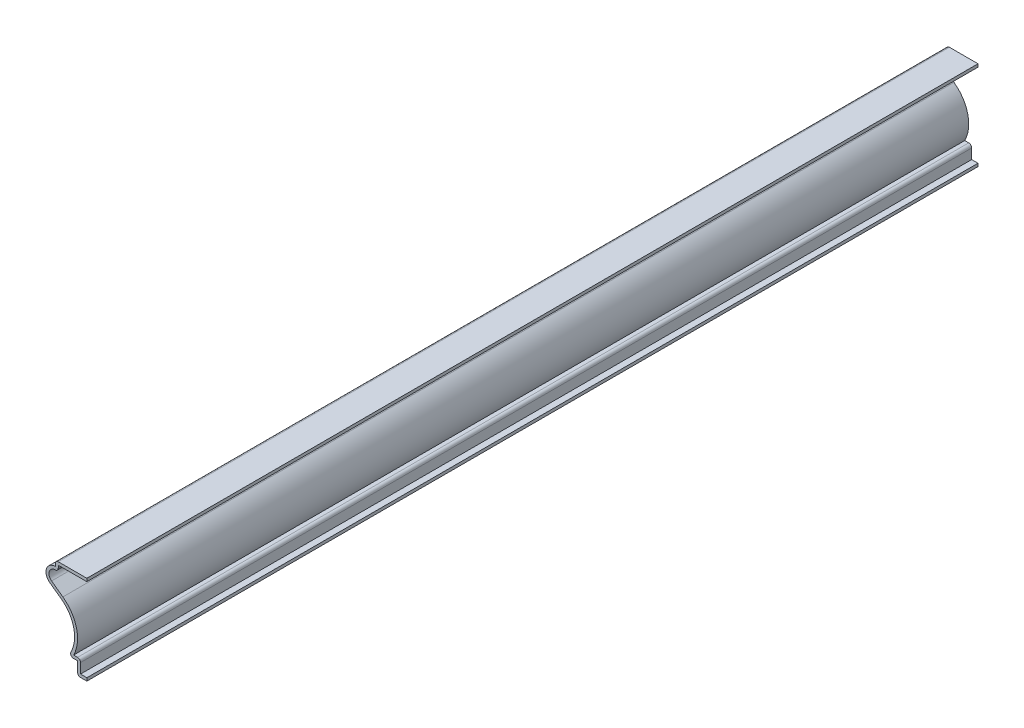
SolidWorks part; units mm, degrees
ref_plane "Front Plane" through (0, 0, 0) normal (0, 0, 1) x (1, 0, 0)
ref_plane "Top Plane" through (0, 0, 0) normal (0, 1, 0) x (1, 0, 0)
ref_plane "Right Plane" through (0, 0, 0) normal (1, 0, 0) x (0, 0, -1)
sketch "Sketch1" plane through (0, 0, 0) normal (0, 0, 1) x (1, 0, 0)
  line L0 (0, 0) -> (0, 38.1) construction
  line L1 (0, 0) -> (-3.9688, 0)
  line L2 (-3.9688, 0) -> (-3.9688, 5.5562)
  line L3 (-3.9688, 5.5562) -> (-7.9375, 5.5562)
  line L4 (0, 38.1) -> (-13.4937, 38.1)
  line L5 (-13.4937, 38.1) -> (-13.4937, 35.7187)
  line L6 (-15.8202, 28.5346) -> (-10.9869, 25.0376)
  line L7 (-3.9688, 5.5562) -> (-3.9688, 27.3259) construction
  arc A0 (-13.4937, 35.7187) -> (-15.8202, 28.5346) centre (-13.4938, 31.75) ccw
  arc A1 (-7.9375, 5.5562) -> (-10.9869, 25.0376) centre (-19.1294, 13.7837) ccw
  arc A2 (-4.8658, 8.6461) -> (-10.2424, 26.0665) centre (-19.1294, 13.7837) ccw construction
  arc A3 (-6.9142, 4.804) -> (-10.2424, 26.0665) centre (-19.1294, 13.7837) ccw construction
  arc A4 (-7.9375, 5.5562) -> (-10.9869, 25.0376) centre (-19.1294, 13.7837) ccw construction
  point P9 (-11.0307, 25.0906)
  point P11 (-19.1933, 13.8047)
  point P12 (-4.8572, 8.641)
  point P15 (-15.4865, 28.3178)
  point P19 (0, 0)
  dimension "D7" = 17.4625
  dimension "D10" = 13.8906
  dimension "D1" = 3.9688
  dimension "D2" = 2.3813
  dimension "D3" = 3.9688
  dimension "D4" = 3.9688
  dimension "D5" = 5.5562
  dimension "D6" = 30.1625
  dimension "D9" = 9.525
  dimension "D8" = 1.27
extrude "Extrude-Thin1" add sketch "Sketch1" against normal blind 381 thin
fillet "Fillet1" radius 1.27 5 edges at (-2.6987, 6.8262, -190.5) (-3.9688, 0, -190.5) (-7.9375, 5.5562, -190.5) (-13.4937, 38.1, -190.5) (-12.2237, 34.1312, -190.5)
